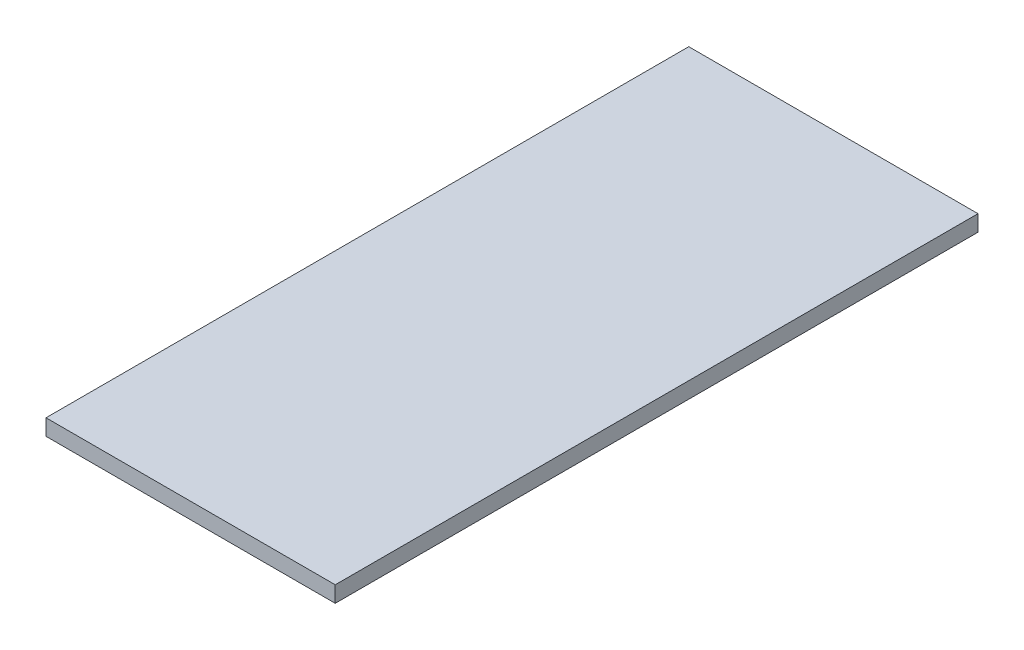
SolidWorks part; units mm, degrees
ref_plane "Front Plane" through (0, 0, 0) normal (0, 0, 1) x (1, 0, 0)
ref_plane "Top Plane" through (0, 0, 0) normal (0, 1, 0) x (1, 0, 0)
ref_plane "Right Plane" through (0, 0, 0) normal (1, 0, 0) x (0, 0, -1)
sketch "Sketch1" plane through (0, 0, 0) normal (0, 1, 0) x (1, 0, 0)
  line L1 (13.5, -30) -> (-13.5, -30)
  line L2 (13.5, -30) -> (13.5, 30)
  line L3 (13.5, 30) -> (-13.5, 30)
  line L4 (-13.5, -30) -> (-13.5, 30)
  line L5 (13.5, -30) -> (-13.5, 30) construction
  line L6 (13.5, 30) -> (-13.5, -30) construction
  point P0 (0, 0)
  dimension "D1" = 60
  dimension "D2" = 27
extrude "Boss-Extrude1" add sketch "Sketch1" along normal blind 1.5
